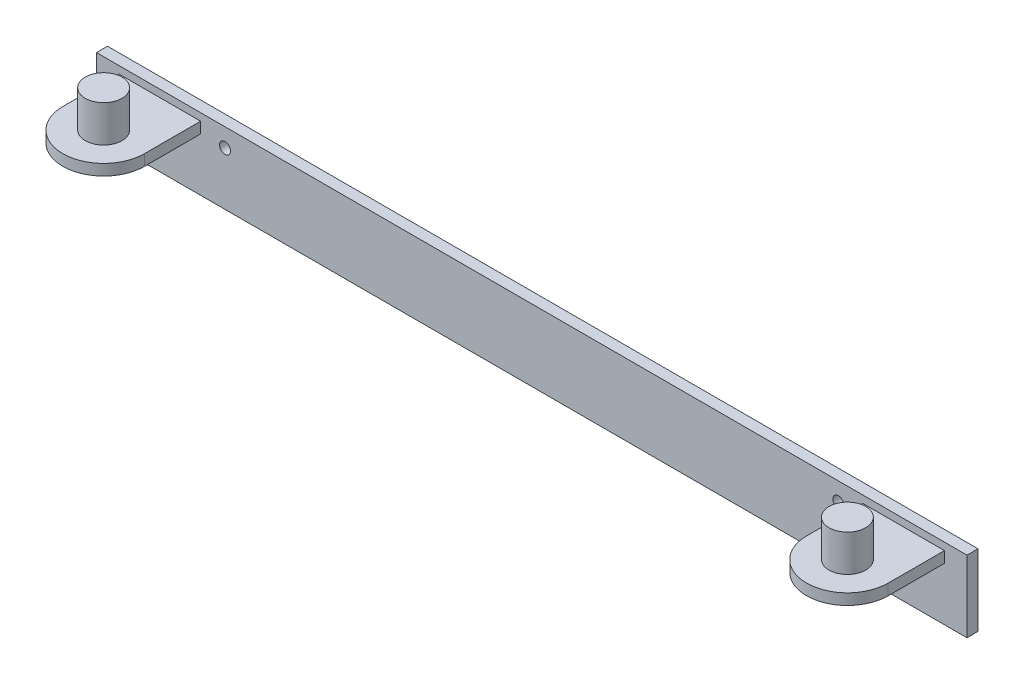
SolidWorks part; units mm, degrees
ref_plane "Plan de face" through (0, 0, 0) normal (0, 0, 1) x (1, 0, 0)
ref_plane "Plan de dessus" through (0, 0, 0) normal (0, 1, 0) x (1, 0, 0)
ref_plane "Plan de droite" through (0, 0, 0) normal (1, 0, 0) x (0, 0, -1)
sketch "Esquisse1" plane through (0, 0, 0) normal (0, 0, 1) x (1, 0, 0)
  line L1 (-58.977, 12.8857) -> (178.033, 12.8857)
  line L2 (-58.977, 12.8857) -> (-58.977, -6.6043)
  line L3 (-58.977, -6.6043) -> (178.033, -6.6043)
  line L4 (178.033, 12.8857) -> (178.033, -6.6043)
  dimension "D1" = 237.01
  dimension "D2" = 19.49
extrude "Boss.-Extru.1" add sketch "Esquisse1" along normal blind 3
ref_plane "Plan1" through (0, 10.8857, 0) normal (0, 1, 0) x (-1, 0, 0)
sketch "Esquisse2" plane through (0, 10.8857, 0) normal (0, 1, 0) x (-1, 0, 0)
  line L0 (52.842, 3) -> (52.842, 18.31)
  line L1 (-178.033, 3) -> (58.977, 3) construction
  line L2 (30.612, 3) -> (30.612, 18.31)
  line L3 (58.977, 3) -> (58.977, 0) construction
  line L4 (52.842, 18.31) -> (30.612, 18.31) construction
  line L5 (52.842, 3) -> (30.612, 3)
  line L6 (-59.528, 18.31) -> (-59.528, -6.8887) construction
  line L7 (-171.898, 3) -> (-149.668, 3)
  line L8 (-171.898, 3) -> (-171.898, 18.31)
  line L9 (-149.668, 3) -> (-149.668, 18.31)
  arc A0 (52.842, 18.31) -> (30.612, 18.31) centre (41.727, 18.31) ccw
  arc A1 (-171.898, 18.31) -> (-149.668, 18.31) centre (-160.783, 18.31) cw
  point P9 (41.727, 18.31)
  point P12 (-160.783, 18.31)
  dimension "D1" = 22.23
  dimension "D2" = 6.135
  dimension "D3" = 15.31
  dimension "D4" = 15.31
  dimension "D5" = 0
  dimension "D6" = 118.505
extrude "Boss.-Extru.2" add sketch "Esquisse2" against normal blind 3
sketch "Esquisse3" plane through (0, 10.8857, 0) normal (0, 1, 0) x (-1, 0, 0)
  line L0 (52.842, 18.31) -> (30.612, 18.31) construction
  circle A0 centre (41.727, 18.31) radius 5
extrude "Boss.-Extru.3" add sketch "Esquisse3" along normal blind 10
sketch "Esquisse4" plane through (0, 10.8857, 0) normal (0, 1, 0) x (-1, 0, 0)
  line L0 (-149.668, 18.31) -> (-171.898, 18.31) construction
  circle A0 centre (-160.783, 18.31) radius 5
extrude "Boss.-Extru.4" add sketch "Esquisse4" along normal blind 10
sketch "Esquisse5" plane through (0, 0, 3) normal (0, 0, 1) x (1, 0, 0)
  line L0 (178.033, 12.8857) -> (-58.977, 12.8857) construction
  line L1 (-58.977, 12.8857) -> (-58.977, -6.6043) construction
  line L2 (178.033, -6.6043) -> (178.033, 12.8857) construction
  circle A0 centre (-23.977, 7.8857) radius 1.5
  circle A1 centre (143.033, 7.8857) radius 1.5
  dimension "D1" = 5
  dimension "D2" = 35
  dimension "D3" = 5
  dimension "D4" = 35
  dimension "D5" = 3
  dimension "D6" = 3
extrude "Enlèv. mat.-Extru.1" cut sketch "Esquisse5" against normal blind 10
